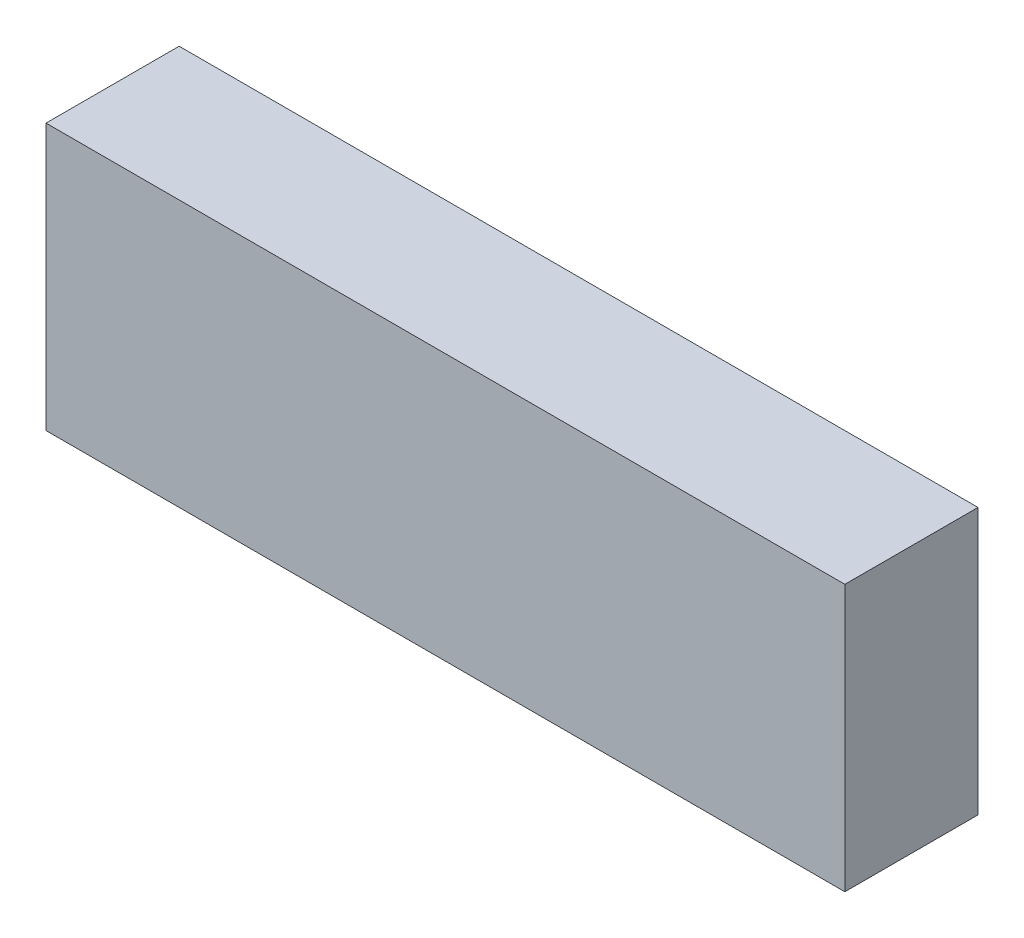
SolidWorks part; units mm, degrees
ref_plane "Plan de face" through (0, 0, 0) normal (0, 0, 1) x (1, 0, 0)
ref_plane "Plan de dessus" through (0, 0, 0) normal (0, 1, 0) x (1, 0, 0)
ref_plane "Plan de droite" through (0, 0, 0) normal (1, 0, 0) x (0, 0, -1)
sketch "Esquisse2" plane through (0, 0, 0) normal (0, 0, 1) x (1, 0, 0)
  line L1 (-81.6563, -23.3808) -> (-51.6563, -23.3808)
  line L2 (-81.6563, -23.3808) -> (-81.6563, -33.3808)
  line L3 (-81.6563, -33.3808) -> (-51.6563, -33.3808)
  line L4 (-51.6563, -23.3808) -> (-51.6563, -33.3808)
  line L5 (-81.6563, -23.3808) -> (-51.6563, -33.3808) construction
  line L6 (-81.6563, -33.3808) -> (-51.6563, -23.3808) construction
  point P0 (-66.6563, -28.3808)
  dimension "D1" = 10
  dimension "D2" = 30
  dimension "D3" = 30
extrude "Boss.-Extru.2" add sketch "Esquisse2" along normal mid plane 5 contours L2 L1 L4 L3
